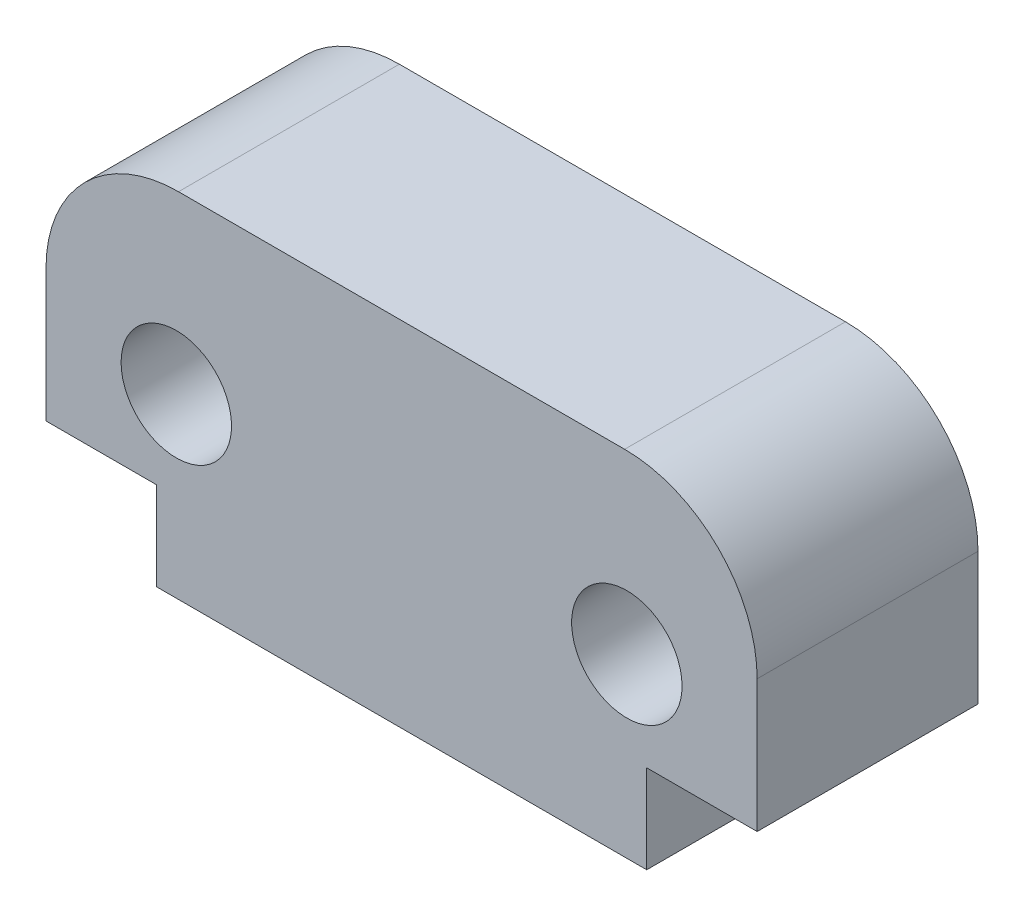
SolidWorks part; units mm, degrees
ref_plane "Front Plane" through (0, 0, 0) normal (0, 0, 1) x (1, 0, 0)
ref_plane "Top Plane" through (0, 0, 0) normal (0, 1, 0) x (1, 0, 0)
ref_plane "Right Plane" through (0, 0, 0) normal (1, 0, 0) x (0, 0, -1)
sketch "Model" plane through (0, 0, 0) normal (0, 0, 1) x (1, 0, 0)
  line L0 (0, 2) -> (-2.5, 2)
  line L1 (-2.5, 2) -> (-2.5, 4.9952)
  line L2 (11.1, 2) -> (11.1, 0)
  line L3 (13.6, 2) -> (13.6, 4.9952)
  line L4 (0, 2) -> (0, 0)
  line L5 (0, 0) -> (11.1, 0)
  line L6 (11.1, 2) -> (13.6, 2)
  line L7 (5.55, 0) -> (5.55, 7.9952) construction
  line L8 (0.5, 7.9952) -> (10.6, 7.9952)
  arc A0 (13.6, 4.9952) -> (10.6, 7.9952) centre (10.6, 4.9952) ccw
  circle A1 centre (0.45, 4) radius 1.25
  circle A2 centre (10.65, 4) radius 1.25
  arc A3 (-2.5, 4.9952) -> (0.5, 7.9952) centre (0.5, 4.9952) cw
  dimension "D5" = 5.1
  dimension "D6" = 2.5
  dimension "D7" = 0.45
  dimension "D1" = 2.5
  dimension "D2" = 2
  dimension "D3" = 2.9952
  dimension "D4" = 3
extrude "Boss-Extrude1" add sketch "Model" along normal blind 5
